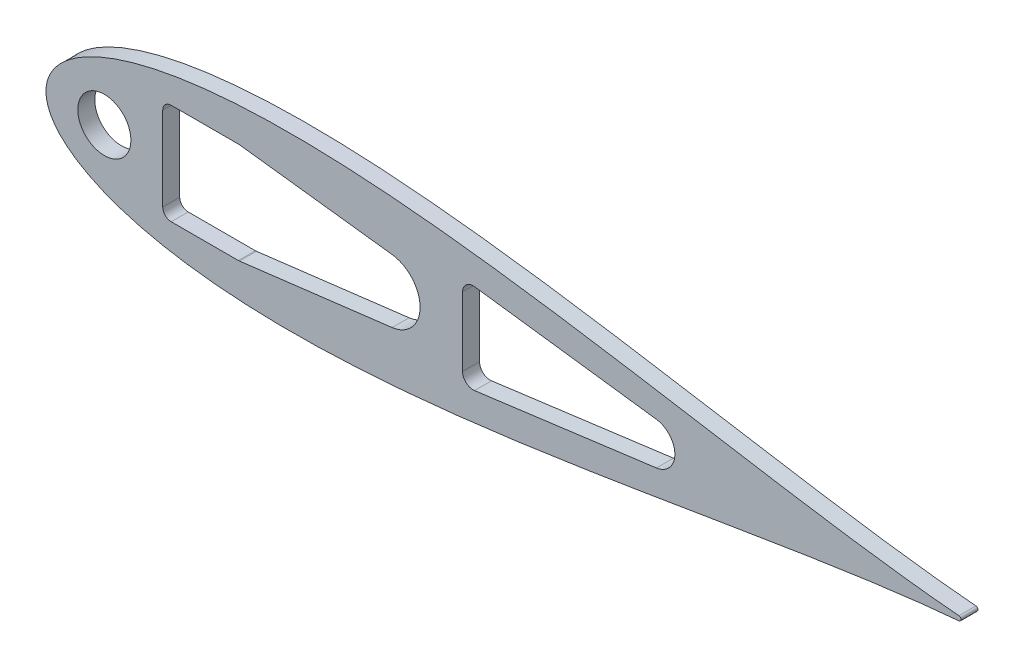
SolidWorks part; units mm, degrees
ref_plane "Front Plane" through (0, 0, 0) normal (0, 0, 1) x (1, 0, 0)
ref_plane "Top Plane" through (0, 0, 0) normal (0, 1, 0) x (1, 0, 0)
ref_plane "Right Plane" through (0, 0, 0) normal (1, 0, 0) x (0, 0, -1)
curve "Curve4"
  spline degree 3 poles (100, 0, 0) (99.8498, 0.0023, 0) (99.4759, 0.008, 0) (99.1023, 0.0238, 0) (98.8789, 0.0332, 0) knots 0 0 0 0 0.401829 1 1 1 1
curve "Curve5"
  spline degree 3 poles (99.3714, -0.0082, 0) (100.2526, 0, 0) (99.3714, 0.0082, 0) (98.8504, 0.035, 0) (97.904, 0.0811, 0) (96.8285, 0.1543, 0) (95.5159, 0.2583, 0) (94.013, 0.3972, 0) (92.313, 0.574, 0) (90.4281, 0.791, 0) (88.3655, 1.0495, 0) (86.1348, 1.3497, 0) (83.7456, 1.691, 0) (81.2082, 2.0715, 0) (78.5335, 2.4886, 0) (75.7326, 2.9386, 0) (72.8172, 3.4168, 0) (69.799, 3.9177, 0) (66.6904, 4.435, 0) (63.5039, 4.9616, 0) (60.2521, 5.4899, 0) (56.948, 6.0119, 0) (53.6049, 6.519, 0) (50.2363, 7.0024, 0) (46.8558, 7.4534, 0) (43.4774, 7.8632, 0) (40.1152, 8.2232, 0) (36.7837, 8.5249, 0) (33.4975, 8.7606, 0) (30.2716, 8.923, 0) (27.1211, 9.0055, 0) (24.0614, 9.0025, 0) (21.108, 8.909, 0) (18.277, 8.7213, 0) (15.5843, 8.4369, 0) (13.0466, 8.0543, 0) (10.6806, 7.5735, 0) (8.5039, 6.996, 0) (6.5349, 6.3253, 0) (4.7933, 5.5673, 0) (3.3001, 4.7321, 0) (2.0777, 3.8366, 0) (1.1467, 2.91, 0) (0.5165, 2.0014, 0) (0.165, 1.1816, 0) (0.0231, 0.524, 0) (-0.0093, 0, 0) (0.0231, -0.524, 0) (0.165, -1.1816, 0) (0.5165, -2.0014, 0) (1.1467, -2.91, 0) (2.0777, -3.8366, 0) (3.3001, -4.7321, 0) (4.7933, -5.5673, 0) (6.5349, -6.3253, 0) (8.5039, -6.996, 0) (10.6806, -7.5735, 0) (13.0466, -8.0543, 0) (15.5843, -8.4369, 0) (18.277, -8.7213, 0) (21.108, -8.909, 0) (24.0614, -9.0025, 0) (27.1211, -9.0055, 0) (30.2716, -8.923, 0) (33.4975, -8.7606, 0) (36.7837, -8.5249, 0) (40.1152, -8.2232, 0) (43.4774, -7.8632, 0) (46.8558, -7.4534, 0) (50.2363, -7.0024, 0) (53.6049, -6.519, 0) (56.948, -6.0119, 0) (60.2521, -5.4899, 0) (63.5039, -4.9616, 0) (66.6904, -4.435, 0) (69.799, -3.9177, 0) (72.8172, -3.4168, 0) (75.7326, -2.9386, 0) (78.5335, -2.4886, 0) (81.2082, -2.0715, 0) (83.7456, -1.691, 0) (86.1348, -1.3497, 0) (88.3655, -1.0495, 0) (90.4281, -0.791, 0) (92.313, -0.574, 0) (94.013, -0.3972, 0) (95.5159, -0.2583, 0) (96.8285, -0.1543, 0) (97.904, -0.0811, 0) (98.8504, -0.035, 0) (99.3714, -0.0082, 0) (100.2526, 0, 0) (99.3714, 0.0082, 0) knots -0.009667 -0.005395 -0.002168 0 0.002168 0.005395 0.009667 0.014967 0.021271 0.028553 0.036781 0.04592 0.055932 0.066773 0.078397 0.090755 0.103793 0.117456 0.131686 0.146422 0.1616 0.177156 0.193024 0.209135 0.225421 0.241812 0.258238 0.274629 0.290914 0.307025 0.322893 0.338448 0.353626 0.368361 0.38259 0.396253 0.40929 0.421647 0.43327 0.444109 0.454119 0.463255 0.471479 0.478755 0.485052 0.490344 0.49461 0.497833 0.5 0.502167 0.50539 0.509656 0.514948 0.521245 0.528521 0.536745 0.545881 0.555891 0.56673 0.578353 0.59071 0.603747 0.61741 0.631639 0.646374 0.661552 0.677107 0.692975 0.709086 0.725371 0.741762 0.758188 0.774579 0.790865 0.806976 0.822844 0.8384 0.853578 0.868314 0.882544 0.896207 0.909245 0.921603 0.933227 0.944068 0.95408 0.963219 0.971447 0.978729 0.985033 0.990333 0.994605 0.997832 1 1.002168 1.005395 1.009667 periodic
sketch "Sketch2" plane through (0, 0, 0) normal (0, 0, 1) x (1, 0, 0)
  line L0 (642.3793, 0) -> (0, 0) construction
  circle A14 centre (642.3793, 0) radius 1.5875 construction
  arc A15 (642.5108, -1.582) -> (642.5108, 1.582) centre (642.3793, 0) ccw
  spline S2 degree 3 poles (666.3448, -0.0547) (672.2538, 0) (666.3448, 0.0547) (662.8509, 0.2344) (656.505, 0.5436) (649.293, 1.0348) (640.4916, 1.7319) (630.4138, 2.6634) (619.0141, 3.8493) (606.375, 5.3044) (592.5439, 7.0376) (577.5855, 9.0506) (561.5643, 11.3389) (544.5497, 13.8907) (526.6141, 16.6877) (507.8326, 19.7051) (488.2827, 22.9117) (468.0444, 26.2704) (447.1994, 29.739) (425.8316, 33.2703) (404.0263, 36.8132) (381.8707, 40.3133) (359.4533, 43.7135) (336.8645, 46.9554) (314.1962, 49.9798) (291.5418, 52.7277) (268.9963, 55.1412) (246.6566, 57.1646) (224.6209, 58.7452) (202.9892, 59.8341) (181.8631, 60.3875) (161.3458, 60.367) (141.542, 59.7399) (122.5581, 58.4818) (104.5023, 56.5743) (87.485, 54.0089) (71.6197, 50.7848) (57.0237, 46.9125) (43.8205, 42.415) (32.1416, 37.3322) (22.1291, 31.7315) (13.9324, 25.7264) (7.6896, 19.5132) (3.4631, 13.4204) (1.1063, 7.9234) (0.1546, 3.5138) (-0.0622, 0) (0.1546, -3.5138) (1.1063, -7.9234) (3.4631, -13.4204) (7.6896, -19.5132) (13.9324, -25.7264) (22.1291, -31.7315) (32.1416, -37.3322) (43.8205, -42.415) (57.0237, -46.9125) (71.6197, -50.7848) (87.485, -54.0089) (104.5023, -56.5743) (122.5581, -58.4818) (141.542, -59.7399) (161.3458, -60.367) (181.8631, -60.3875) (202.9892, -59.8341) (224.6209, -58.7452) (246.6566, -57.1646) (268.9963, -55.1412) (291.5418, -52.7277) (314.1962, -49.9798) (336.8645, -46.9554) (359.4533, -43.7135) (381.8707, -40.3133) (404.0263, -36.8132) (425.8316, -33.2703) (447.1994, -29.739) (468.0444, -26.2704) (488.2827, -22.9117) (507.8326, -19.7051) (526.6141, -16.6877) (544.5497, -13.8907) (561.5643, -11.3389) (577.5855, -9.0506) (592.5439, -7.0376) (606.375, -5.3044) (619.0141, -3.8493) (630.4138, -2.6634) (640.4916, -1.7319) (649.293, -1.0348) (656.505, -0.5436) (662.8509, -0.2344) (666.3448, -0.0547) (672.2538, 0) (666.3448, 0.0547) knots -0.009667 -0.005395 -0.002168 0 0.002168 0.005395 0.009667 0.014967 0.021271 0.028553 0.036781 0.04592 0.055932 0.066773 0.078397 0.090755 0.103793 0.117456 0.131686 0.146422 0.1616 0.177156 0.193024 0.209135 0.225421 0.241812 0.258238 0.274629 0.290914 0.307025 0.322893 0.338448 0.353626 0.368361 0.38259 0.396253 0.40929 0.421647 0.43327 0.444109 0.454119 0.463255 0.471479 0.478755 0.485052 0.490344 0.49461 0.497833 0.5 0.502167 0.50539 0.509656 0.514948 0.521245 0.528521 0.536745 0.545881 0.555891 0.56673 0.578353 0.59071 0.603747 0.61741 0.631639 0.646374 0.661552 0.677107 0.692975 0.709086 0.725371 0.741762 0.758188 0.774579 0.790865 0.806976 0.822844 0.8384 0.853578 0.868314 0.882544 0.896207 0.909245 0.921603 0.933227 0.944068 0.95408 0.963219 0.971447 0.978729 0.985033 0.990333 0.994605 0.997832 1 1.002168 1.005395 1.009667 only from (670.56, 0) to (670.56, 0)
  point P8 (1.2169, -4.6585)
  point P10 (1.2169, 4.6585)
  dimension "D10" = 3.175
extrude "Boss-Extrude1" add sketch "Sketch2" along normal blind 5.4737
extrude "Cut-Extrude4" cut sketch "Sketch7" against normal through all
sketch "Sketch7" plane through (327.9592, -13.7514, 6.35) normal (0, 0, 1) x (1, 0, 0)
  line L1 (-154.9852, -16.7286) -> (-66.0852, -16.7286)
  line L2 (-154.9852, -16.7286) -> (-154.9852, 44.2314)
  line L3 (-154.9852, 44.2314) -> (-66.0852, 44.2314)
  line L4 (-66.0852, -16.7286) -> (-66.0852, 44.2314)
  line L5 (-154.9852, -16.7286) -> (-66.0852, 44.2314) construction
  line L6 (-154.9852, 44.2314) -> (-66.0852, -16.7286) construction
  point P0 (-110.5352, 13.7514)
extrude "Cut-Extrude5" cut sketch "Sketch8" against normal through all
sketch "Sketch8" plane through (327.9592, -13.7514, 6.35) normal (0, 0, 1) x (1, 0, 0)
  circle A0 centre (314.9285, 13.7514) radius 1.2446
scale "Scale1" bodies to scale 101 scale about origin uniform scaling yes scale factor 0.425
sketch "Sketch11" plane through (0, 0, 0) normal (0, 0, -1) x (-1, 0, 0)
  arc A1 (-273.0671, 0.6724) -> (-273.0671, -0.6724) centre (-273.0112, 0) ccw
  arc A2 (-273.0671, 0.6724) -> (-273.0671, -0.6724) centre (-273.0112, 0) ccw
  spline S1 degree 3 poles (1718.5375, -180.9874) (-398.2556, -6.3048) (-328.2302, 4.4419) (-267.9259, -1.1319) (-263.081, -1.6359) (-257.7094, -2.2544) (-251.8312, -2.991) (-245.4738, -3.8465) (-238.6648, -4.819) (-231.4336, -5.9035) (-223.811, -7.0923) (-215.8289, -8.3747) (-207.5202, -9.7375) (-198.9189, -11.1649) (-190.0598, -12.6391) (-180.9784, -14.1399) (-171.7112, -15.6456) (-162.295, -17.1331) (-152.7677, -18.5782) (-143.1674, -19.9561) (-133.5334, -21.2414) (-123.9053, -22.4093) (-114.3234, -23.435) (-104.829, -24.295) (-95.4639, -24.9667) (-86.2704, -25.4295) (-77.2918, -25.6647) (-68.572, -25.656) (-60.1554, -25.3895) (-52.0872, -24.8547) (-44.4135, -24.0441) (-37.1811, -22.9538) (-30.4384, -21.5835) (-24.2351, -19.9378) (-18.6237, -18.0264) (-13.6602, -15.8662) (-9.4049, -13.4859) (-5.9213, -10.9337) (-3.2681, -8.2931) (-1.4718, -5.7037) (-0.4702, -3.3674) (-0.0657, -1.4934) (0.0264, 0) (-0.0657, 1.4934) (-0.4702, 3.3674) (-1.4718, 5.7037) (-3.2681, 8.2931) (-5.9213, 10.9337) (-9.4049, 13.4859) (-13.6602, 15.8662) (-18.6237, 18.0264) (-24.2351, 19.9378) (-30.4384, 21.5835) (-37.1811, 22.9538) (-44.4135, 24.0441) (-52.0872, 24.8547) (-60.1554, 25.3895) (-68.572, 25.656) (-77.2918, 25.6647) (-86.2704, 25.4295) (-95.4639, 24.9667) (-104.829, 24.295) (-114.3234, 23.435) (-123.9053, 22.4093) (-133.5334, 21.2414) (-143.1674, 19.9561) (-152.7677, 18.5782) (-162.295, 17.1331) (-171.7112, 15.6456) (-180.9784, 14.1399) (-190.0598, 12.6391) (-198.9189, 11.1649) (-207.5202, 9.7375) (-215.8289, 8.3747) (-223.811, 7.0923) (-231.4336, 5.9035) (-238.6648, 4.819) (-245.4738, 3.8465) (-251.8312, 2.991) (-257.7094, 2.2544) (-263.081, 1.6359) (-267.9259, 1.1319) (-328.2298, -4.4418) (-398.2547, 6.3046) (1718.4938, 180.9838) knots -0.270354 -0.270354 -0.270354 -0.270354 0.021271 0.028553 0.036781 0.04592 0.055932 0.066773 0.078397 0.090755 0.103793 0.117456 0.131686 0.146422 0.1616 0.177156 0.193024 0.209135 0.225421 0.241812 0.258238 0.274629 0.290914 0.307025 0.322893 0.338448 0.353626 0.368361 0.38259 0.396253 0.40929 0.421647 0.43327 0.444109 0.454119 0.463255 0.471479 0.478755 0.485052 0.490344 0.49461 0.497833 0.5 0.502167 0.50539 0.509656 0.514948 0.521245 0.528521 0.536745 0.545881 0.555891 0.56673 0.578353 0.59071 0.603747 0.61741 0.631639 0.646374 0.661552 0.677107 0.692975 0.709086 0.725371 0.741762 0.758188 0.774579 0.790865 0.806976 0.822844 0.8384 0.853578 0.868314 0.882544 0.896207 0.909245 0.921603 0.933227 0.944068 0.95408 0.963219 0.971447 0.978729 1.270352 1.270352 1.270352 1.270352 only from (-273.0671, -0.6724) to (-273.0671, 0.6724)
  spline S2 degree 3 poles (-273.0671, -0.6724) (-272.8472, -0.6907) (-271.1898, -0.8303) (-267.9259, -1.1319) (-263.081, -1.6359) (-257.7094, -2.2544) (-251.8312, -2.991) (-245.4738, -3.8465) (-238.6648, -4.819) (-231.4336, -5.9035) (-223.811, -7.0923) (-215.8289, -8.3747) (-207.5202, -9.7375) (-198.9189, -11.1649) (-190.0598, -12.6391) (-180.9784, -14.1399) (-171.7112, -15.6456) (-162.295, -17.1331) (-152.7677, -18.5782) (-143.1674, -19.9561) (-133.5334, -21.2414) (-123.9053, -22.4093) (-114.3234, -23.435) (-104.829, -24.295) (-95.4639, -24.9667) (-86.2704, -25.4295) (-77.2918, -25.6647) (-68.572, -25.656) (-60.1554, -25.3895) (-52.0872, -24.8547) (-44.4135, -24.0441) (-37.1811, -22.9538) (-30.4384, -21.5835) (-24.2351, -19.9378) (-18.6237, -18.0264) (-13.6602, -15.8662) (-9.4049, -13.4859) (-5.9213, -10.9337) (-3.2681, -8.2931) (-1.4718, -5.7037) (-0.4702, -3.3674) (-0.0657, -1.4934) (0.0264, 0) (-0.0657, 1.4934) (-0.4702, 3.3674) (-1.4718, 5.7037) (-3.2681, 8.2931) (-5.9213, 10.9337) (-9.4049, 13.4859) (-13.6602, 15.8662) (-18.6237, 18.0264) (-24.2351, 19.9378) (-30.4384, 21.5835) (-37.1811, 22.9538) (-44.4135, 24.0441) (-52.0872, 24.8547) (-60.1554, 25.3895) (-68.572, 25.656) (-77.2918, 25.6647) (-86.2704, 25.4295) (-95.4639, 24.9667) (-104.829, 24.295) (-114.3234, 23.435) (-123.9053, 22.4093) (-133.5334, 21.2414) (-143.1674, 19.9561) (-152.7677, 18.5782) (-162.295, 17.1331) (-171.7112, 15.6456) (-180.9784, 14.1399) (-190.0598, 12.6391) (-198.9189, 11.1649) (-207.5202, 9.7375) (-215.8289, 8.3747) (-223.811, 7.0923) (-231.4336, 5.9035) (-238.6648, 4.819) (-245.4738, 3.8465) (-251.8312, 2.991) (-257.7094, 2.2544) (-263.081, 1.6359) (-267.9259, 1.1319) (-271.1898, 0.8303) (-272.8472, 0.6907) (-273.0671, 0.6724) knots 0.020157 0.020157 0.020157 0.020157 0.021271 0.028553 0.036781 0.04592 0.055932 0.066773 0.078397 0.090755 0.103793 0.117456 0.131686 0.146422 0.1616 0.177156 0.193024 0.209135 0.225421 0.241812 0.258238 0.274629 0.290914 0.307025 0.322893 0.338448 0.353626 0.368361 0.38259 0.396253 0.40929 0.421647 0.43327 0.444109 0.454119 0.463255 0.471479 0.478755 0.485052 0.490344 0.49461 0.497833 0.5 0.502167 0.50539 0.509656 0.514948 0.521245 0.528521 0.536745 0.545881 0.555891 0.56673 0.578353 0.59071 0.603747 0.61741 0.631639 0.646374 0.661552 0.677107 0.692975 0.709086 0.725371 0.741762 0.758188 0.774579 0.790865 0.806976 0.822844 0.8384 0.853578 0.868314 0.882544 0.896207 0.909245 0.921603 0.933227 0.944068 0.95408 0.963219 0.971447 0.978729 0.979843 0.979843 0.979843 0.979843
  dimension "D1" = 0
extrude "Boss-Extrude2" add sketch "Sketch11" against normal blind 5.08
sketch "Sketch10" plane through (0, 0, 0) normal (0, 0, 1) x (1, 0, 0)
  line L1 (34.925, -15.0812) -> (60.0922, -15.0812)
  line L2 (34.925, -15.0812) -> (34.925, 15.0812)
  line L3 (34.925, 15.0812) -> (60.0922, 15.0812)
  line L4 (60.0922, -15.0812) -> (60.0922, 15.0812)
  line L5 (34.925, -15.0812) -> (60.0922, 15.0812) construction
  line L6 (34.925, 15.0812) -> (60.0922, -15.0812) construction
  arc A2 (273.0671, -0.6724) -> (273.0671, 0.6724) centre (273.0112, 0) ccw
  arc A3 (273.0671, -0.6724) -> (273.0671, 0.6724) centre (273.0112, 0) ccw construction
  spline S1 degree 3 poles (-722.2115, 97.2029) (372.3157, 2.8343) (317.1919, -3.4216) (267.9259, 1.1319) (263.081, 1.6359) (257.7094, 2.2544) (251.8312, 2.991) (245.4738, 3.8465) (238.6648, 4.819) (231.4336, 5.9035) (223.811, 7.0923) (215.8289, 8.3747) (207.5202, 9.7375) (198.9189, 11.1649) (190.0598, 12.6391) (180.9784, 14.1399) (171.7112, 15.6456) (162.295, 17.1331) (152.7677, 18.5782) (143.1674, 19.9561) (133.5334, 21.2414) (123.9053, 22.4093) (114.3234, 23.435) (104.829, 24.295) (95.4639, 24.9667) (86.2704, 25.4295) (77.2918, 25.6647) (68.572, 25.656) (60.1554, 25.3895) (52.0872, 24.8547) (44.4135, 24.0441) (37.1811, 22.9538) (30.4384, 21.5835) (24.2351, 19.9378) (18.6237, 18.0264) (13.6602, 15.8662) (9.4049, 13.4859) (5.9213, 10.9337) (3.2681, 8.2931) (1.4718, 5.7037) (0.4702, 3.3674) (0.0657, 1.4934) (-0.0264, 0) (0.0657, -1.4934) (0.4702, -3.3674) (1.4718, -5.7037) (3.2681, -8.2931) (5.9213, -10.9337) (9.4049, -13.4859) (13.6602, -15.8662) (18.6237, -18.0264) (24.2351, -19.9378) (30.4384, -21.5835) (37.1811, -22.9538) (44.4135, -24.0441) (52.0872, -24.8547) (60.1554, -25.3895) (68.572, -25.656) (77.2918, -25.6647) (86.2704, -25.4295) (95.4639, -24.9667) (104.829, -24.295) (114.3234, -23.435) (123.9053, -22.4093) (133.5334, -21.2414) (143.1674, -19.9561) (152.7677, -18.5782) (162.295, -17.1331) (171.7112, -15.6456) (180.9784, -14.1399) (190.0598, -12.6391) (198.9189, -11.1649) (207.5202, -9.7375) (215.8289, -8.3747) (223.811, -7.0923) (231.4336, -5.9035) (238.6648, -4.819) (245.4738, -3.8465) (251.8312, -2.991) (257.7094, -2.2544) (263.081, -1.6359) (267.9259, -1.1319) (317.1911, 3.4215) (372.3138, -2.8341) (-722.1546, -97.198) knots -0.214135 -0.214135 -0.214135 -0.214135 0.021271 0.028553 0.036781 0.04592 0.055932 0.066773 0.078397 0.090755 0.103793 0.117456 0.131686 0.146422 0.1616 0.177156 0.193024 0.209135 0.225421 0.241812 0.258238 0.274629 0.290914 0.307025 0.322893 0.338448 0.353626 0.368361 0.38259 0.396253 0.40929 0.421647 0.43327 0.444109 0.454119 0.463255 0.471479 0.478755 0.485052 0.490344 0.49461 0.497833 0.5 0.502167 0.50539 0.509656 0.514948 0.521245 0.528521 0.536745 0.545881 0.555891 0.56673 0.578353 0.59071 0.603747 0.61741 0.631639 0.646374 0.661552 0.677107 0.692975 0.709086 0.725371 0.741762 0.758188 0.774579 0.790865 0.806976 0.822844 0.8384 0.853578 0.868314 0.882544 0.896207 0.909245 0.921603 0.933227 0.944068 0.95408 0.963219 0.971447 0.978729 1.214131 1.214131 1.214131 1.214131 only from (273.0671, 0.6724) to (273.0671, -0.6724)
  point P0 (47.5086, 0)
  dimension "D1" = 25.1672
  dimension "D2" = 34.925
  dimension "D5" = 30.1625
  dimension "D3" = 0
extrude "Cut-Extrude6" cut sketch "Sketch10" along normal through all
fillet "Fillet1" radius 2.54 4 edges at (60.0922, -15.0812, 2.54) (34.925, -15.0812, 2.54) (34.925, 15.0812, 2.54) (60.0922, 15.0812, 2.54)
hole_wizard "#8 Clearance Hole1" positions "Sketch12" profile "Sketch13" hole size "#8" standard "ANSI Inch"
sketch "Sketch12" plane through (0, 0, 5.08) normal (0, 0, 1) x (1, 0, 0)
  line L0 (76.2, 0) -> (0, 0) construction
  line L2 (31.75, 8.8646) -> (31.75, -8.8646) construction
  point P0 (12.7, 0)
  point P2 (76.2, 0)
  dimension "D1" = 19.05
  dimension "D2" = 44.45
sketch "Sketch13" plane through (12.7, 0, 5.08) normal (1, 0, 0) x (0, -1, 0)
  line L0 (0, 0) -> (0, 5.08)
  line L1 (0, 5.08) -> (2.2479, 5.08)
  line L2 (2.2479, 5.08) -> (2.2479, 0)
  line L5 (2.2479, 0) -> (0, 0)
  line L11 (0, -6.35) -> (0, 107.95) construction
  dimension "Thru Hole Dia." = 4.4958
  dimension "Thru Hole Depth" = 5.08
sketch "Sketch15" plane through (0, 0, 5.08) normal (0, 0, 1) x (1, 0, 0)
  line L0 (35.6689, 14.3373) -> (59.3482, -14.3373)
  line L1 (24.0679, 12.7) -> (74.8679, -12.7) construction
  line L2 (26.6079, 12.7) -> (72.3279, 12.7)
  line L3 (24.0679, 10.16) -> (24.0679, -10.16)
  line L4 (26.6079, -12.7) -> (72.3279, -12.7)
  line L5 (74.8679, 10.16) -> (74.8679, -10.16)
  circle A0 centre (47.5086, 0) radius 13.716
  arc A1 (37.465, 15.0812) -> (34.925, 12.5412) centre (37.465, 12.5412) ccw construction
  arc A2 (57.5522, -15.0812) -> (60.0922, -12.5412) centre (57.5522, -12.5412) ccw construction
  arc A3 (72.3279, 12.7) -> (74.8679, 10.16) centre (72.3279, 10.16) cw
  arc A4 (74.8679, -10.16) -> (72.3279, -12.7) centre (72.3279, -10.16) cw
  arc A5 (26.6079, -12.7) -> (24.0679, -10.16) centre (26.6079, -10.16) cw
  arc A6 (26.6079, 12.7) -> (24.0679, 10.16) centre (26.6079, 10.16) ccw
  point P10 (49.4679, 0)
  point P18 (74.8679, 12.7)
  dimension "D1" = 27.432
  dimension "D4" = 2.54
  dimension "D2" = 50.8
  dimension "D3" = 25.4
sketch "Sketch16" plane through (0, 0, 5.08) normal (0, 0, 1) x (1, 0, 0)
  line L0 (102.3726, 0) -> (100.5946, 0) construction
  line L1 (102.3726, -9.525) -> (100.5946, -9.525)
  line L2 (102.3726, 9.525) -> (100.5946, 9.525)
  arc A0 (102.3726, -9.525) -> (102.3726, 9.525) centre (102.3726, 0) ccw
  arc A1 (100.5946, 9.525) -> (100.5946, -9.525) centre (100.5946, 0) ccw
  point P3 (101.4836, 0)
  dimension "D1" = 9.525
  dimension "D2" = 1.778
  dimension "D3" = 53.975
extrude "Cut-Extrude8" cut sketch "Sketch16" against normal through all
sketch "Sketch18" plane through (0, 0, 5.08) normal (0, 0, 1) x (1, 0, 0)
  line L2 (57.8617, 15.0623) -> (103.5335, 9.454)
  line L4 (103.5335, -9.454) -> (57.8617, -15.0623)
  line L5 (60.0922, -12.5412) -> (60.0922, 12.5412) construction
  line L8 (60.0922, -12.5412) -> (60.0922, 12.5412)
  arc A0 (60.0922, 12.5412) -> (57.5522, 15.0812) centre (57.5522, 12.5412) ccw construction
  arc A3 (102.3726, -9.525) -> (102.3726, 9.525) centre (102.3726, 0) ccw construction
  arc A4 (57.5522, -15.0812) -> (60.0922, -12.5412) centre (57.5522, -12.5412) ccw construction
  arc A6 (103.5335, -9.454) -> (103.5335, 9.454) centre (102.3726, 0) ccw
  arc A8 (57.8617, -15.0623) -> (60.0922, -12.5412) centre (57.5522, -12.5412) ccw
  arc A9 (60.0922, 12.5412) -> (57.8617, 15.0623) centre (57.5522, 12.5412) ccw
extrude "Cut-Extrude9" cut sketch "Sketch18" against normal through all
sketch "Sketch19" plane through (0, 0, 5.08) normal (0, 0, 1) x (1, 0, 0)
  line L0 (34.925, 0) -> (0, 0) construction
  line L1 (34.925, 12.5412) -> (34.925, -12.5412) construction
  line L2 (128.187, 13.4562) -> (182.5764, 6.2957)
  line L3 (182.5764, -6.2957) -> (128.187, -13.4562)
  line L4 (124.5976, -10.3083) -> (124.5976, 10.3083)
  circle A0 centre (17.4625, 0) radius 7.9375
  arc A1 (182.5764, -6.2957) -> (182.5764, 6.2957) centre (181.7476, 0) ccw
  arc A2 (124.5976, -10.3083) -> (128.187, -13.4562) centre (127.7726, -10.3083) ccw
  arc A3 (128.187, 13.4562) -> (124.5976, 10.3083) centre (127.7726, 10.3083) ccw
  arc A4 (103.5335, -9.454) -> (103.5335, 9.454) centre (102.3726, 0) ccw construction
  point P16 (0, 0)
  point P20 (111.8976, 0)
  dimension "D1" = 6.35
  dimension "D2" = 3.175
  dimension "D3" = 3.175
  dimension "D7" = 15.875
  dimension "D4" = 15
  dimension "D5" = 12.7
  dimension "D6" = 69.85
extrude "Cut-Extrude10" cut sketch "Sketch19" against normal through all contours A0 | L4 A3 L2 A1 L3 A2
equation "\"0.5n\"=0"
equation "\"D1@Sketch10\"=0.898/cos(25deg)"
